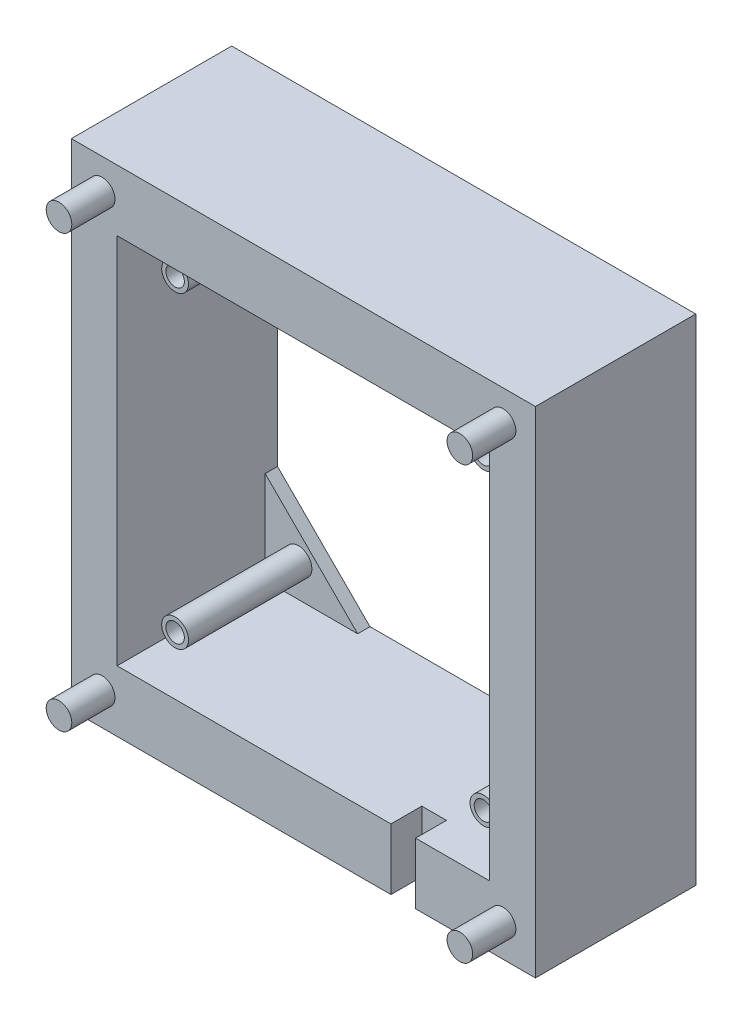
SolidWorks part; units mm, degrees
ref_plane "Alzado" through (0, 0, 0) normal (0, 0, 1) x (1, 0, 0)
ref_plane "Planta" through (0, 0, 0) normal (0, 1, 0) x (1, 0, 0)
ref_plane "Vista lateral" through (0, 0, 0) normal (1, 0, 0) x (0, 0, -1)
sketch "Croquis1" plane through (0, 0, 0) normal (0, 0, 1) x (1, 0, 0)
  line L1 (-95.8163, 28.0569) -> (-20.5663, 28.0569)
  line L2 (-95.8163, 28.0569) -> (-95.8163, -52.1931)
  line L3 (-95.8163, -52.1931) -> (-20.5663, -52.1931)
  line L4 (-20.5663, 28.0569) -> (-20.5663, -52.1931)
  line L5 (-88.3913, 18.1319) -> (-27.9913, 18.1319)
  line L6 (-88.3913, 18.1319) -> (-88.3913, -42.2681)
  line L7 (-88.3913, -42.2681) -> (-27.9913, -42.2681)
  line L8 (-27.9913, 18.1319) -> (-27.9913, -42.2681)
  dimension "D1" = 75.25
  dimension "D2" = 80.25
  dimension "D3" = 60.4
  dimension "D4" = 60.4
  dimension "D5" = 9.925
  dimension "D6" = 7.425
extrude "Saliente-Extruir1" add sketch "Croquis1" along normal blind 24
sketch "Croquis2" plane through (0, 0, 24) normal (0, 0, 1) x (1, 0, 0)
  line L0 (-95.8163, 28.0569) -> (-95.8163, -52.1931) construction
  line L5 (-20.5663, 28.0569) -> (-95.8163, 28.0569) construction
  circle A0 centre (-90.8163, 23.0569) radius 2.075
  circle A1 centre (-25.8163, 23.0569) radius 2.075
  circle A2 centre (-25.8163, -46.9431) radius 2.075
  circle A3 centre (-90.8163, -46.9431) radius 2.075
  dimension "D1" = 2
  dimension "D3" = 5
  dimension "D4" = 5
  dimension "D2" = 2
extrude "Saliente-Extruir2" add sketch "Croquis2" along normal blind 7
sketch "Croquis3" plane through (0, 0, 0) normal (0, 0, -1) x (-1, 0, 0)
  line L0 (20.5663, -19.8431) -> (20.5663, -52.1931)
  line L2 (20.5663, -52.1931) -> (52.9163, -52.1931)
  line L4 (27.9913, -42.2681) -> (88.3913, 18.1319) construction
  line L5 (88.3913, 18.1319) -> (88.3913, -42.2681) construction
  line L6 (95.8163, -52.1931) -> (20.5663, -52.1931) construction
  line L7 (52.9163, -52.1931) -> (20.5663, -19.8431)
  line L8 (20.5663, -52.1931) -> (20.5663, 28.0569) construction
  line L9 (88.3913, -42.2681) -> (27.9913, 18.1319) construction
  line L10 (95.8163, -4.2931) -> (95.8163, 28.0569)
  line L11 (95.8163, 28.0569) -> (63.4663, 28.0569)
  line L12 (63.4663, 28.0569) -> (95.8163, -4.2931)
  line L13 (95.8163, -19.8431) -> (63.4663, -52.1931)
  line L15 (63.4663, -52.1931) -> (95.8163, -52.1931)
  line L16 (95.8163, -52.1931) -> (95.8163, -19.8431)
  line L18 (27.9913, -42.2681) -> (27.9913, 18.1319) construction
  line L19 (20.5663, -4.2931) -> (52.9163, 28.0569)
  line L20 (20.5663, 28.0569) -> (95.8163, 28.0569) construction
  line L21 (52.9163, 28.0569) -> (20.5663, 28.0569)
  line L22 (20.5663, 28.0569) -> (20.5663, -4.2931)
  circle A0 centre (32.9913, 13.1319) radius 1.5
  circle A1 centre (82.9913, 13.1319) radius 1.5
  circle A2 centre (82.9913, -36.8681) radius 1.5
  circle A3 centre (32.9913, -36.8681) radius 1.5
  point P25 (58.1913, -12.0681)
  point P27 (58.1913, -12.0681)
  point P36 (58.1913, -12.0681)
  dimension "D3" = 5
  dimension "D1" = 2
  dimension "D2" = 2
  dimension "D4" = 2
  dimension "D5" = 2
extrude "Saliente-Extruir3" add sketch "Croquis3" along normal blind 2
sketch "Croquis4" plane through (0, 0, 0) normal (0, 0, 1) x (1, 0, 0)
  circle A0 centre (-82.9913, 13.1319) radius 2.175
  circle A1 centre (-82.9913, 13.1319) radius 1.5
  circle A2 centre (-32.9913, 13.1319) radius 2.175
  circle A3 centre (-32.9913, 13.1319) radius 1.5
  circle A4 centre (-32.9913, -36.8681) radius 2.175
  circle A5 centre (-32.9913, -36.8681) radius 1.5
  circle A6 centre (-82.9913, -36.8681) radius 2.175
  circle A7 centre (-82.9913, -36.8681) radius 1.5
  dimension "D1" = 2
  dimension "D2" = 2
extrude "Saliente-Extruir4" add sketch "Croquis4" along normal blind 20
sketch "Croquis5" plane through (0, -42.2681, 0) normal (0, 1, 0) x (1, 0, 0)
  line L0 (-88.3913, -24) -> (-27.9913, -24) construction
  line L1 (-39.9913, -24) -> (-43.9913, -24)
  line L2 (-39.9913, -24) -> (-39.9913, -19)
  line L3 (-39.9913, -19) -> (-43.9913, -19)
  line L4 (-43.9913, -24) -> (-43.9913, -19)
  line L5 (-27.9913, -24) -> (-27.9913, 0) construction
  dimension "D1" = 12
  dimension "D2" = 4
  dimension "D3" = 5
extrude "Cortar-Extruir1" cut sketch "Croquis5" against normal up to vertex (9.925 mm away) up to point (-95.8163, -52.1931, 24)
sketch "Croquis6" plane through (0, 0, 0) normal (0, 0, -1) x (-1, 0, 0)
  line L0 (42.9913, 18.1319) -> (52.9163, 28.0569)
  line L1 (52.9163, 28.0569) -> (63.4663, 28.0569)
  line L2 (63.4663, 28.0569) -> (73.3913, 18.1319)
  line L3 (73.3913, 18.1319) -> (42.9913, 18.1319)
  line L4 (27.9913, 3.1319) -> (27.9913, -27.2681)
  line L5 (27.9913, -27.2681) -> (20.5663, -19.8431)
  line L6 (20.5663, -19.8431) -> (20.5663, -4.2931)
  line L7 (20.5663, -4.2931) -> (27.9913, 3.1319)
  line L8 (42.9913, -42.2681) -> (52.9163, -52.1931)
  line L9 (52.9163, -52.1931) -> (63.4663, -52.1931)
  line L10 (63.4663, -52.1931) -> (73.3913, -42.2681)
  line L11 (73.3913, -42.2681) -> (42.9913, -42.2681)
  line L12 (88.3913, -27.2681) -> (88.3913, 3.1319)
  line L13 (88.3913, 3.1319) -> (95.8163, -4.2931)
  line L14 (95.8163, -4.2931) -> (95.8163, -19.8431)
  line L15 (95.8163, -19.8431) -> (88.3913, -27.2681)
extrude "Saliente-Extruir5" add sketch "Croquis6" along normal up to vertex (2 mm away)
